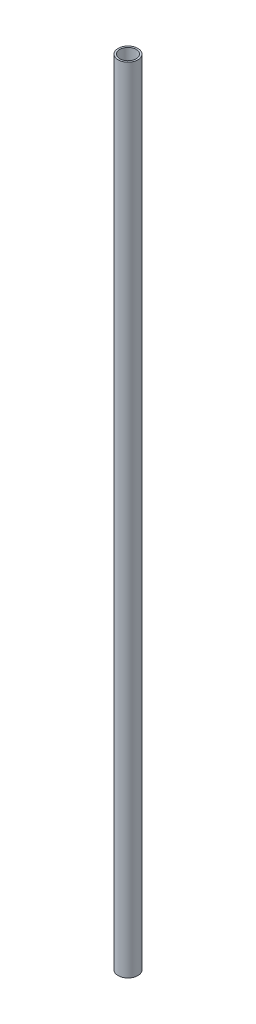
SolidWorks part; units mm, degrees
ref_plane "前视基准面" through (0, 0, 0) normal (0, 0, 1) x (1, 0, 0)
ref_plane "上视基准面" through (0, 0, 0) normal (0, 1, 0) x (1, 0, 0)
ref_plane "右视基准面" through (0, 0, 0) normal (1, 0, 0) x (0, 0, -1)
sketch "草图1" plane through (0, 0, 0) normal (0, 1, 0) x (1, 0, 0)
  circle A0 centre (0, 0) radius 4.25
  dimension "D1" = 8.5
extrude "凸台-拉伸1" add sketch "草图1" along normal blind 340
sketch "草图2" plane through (0, 0, 0) normal (0, 1, 0) x (1, 0, 0)
  circle A0 centre (0, 0) radius 3.5
  dimension "D1" = 7
extrude "切除-拉伸1" cut sketch "草图2" along normal blind 494
